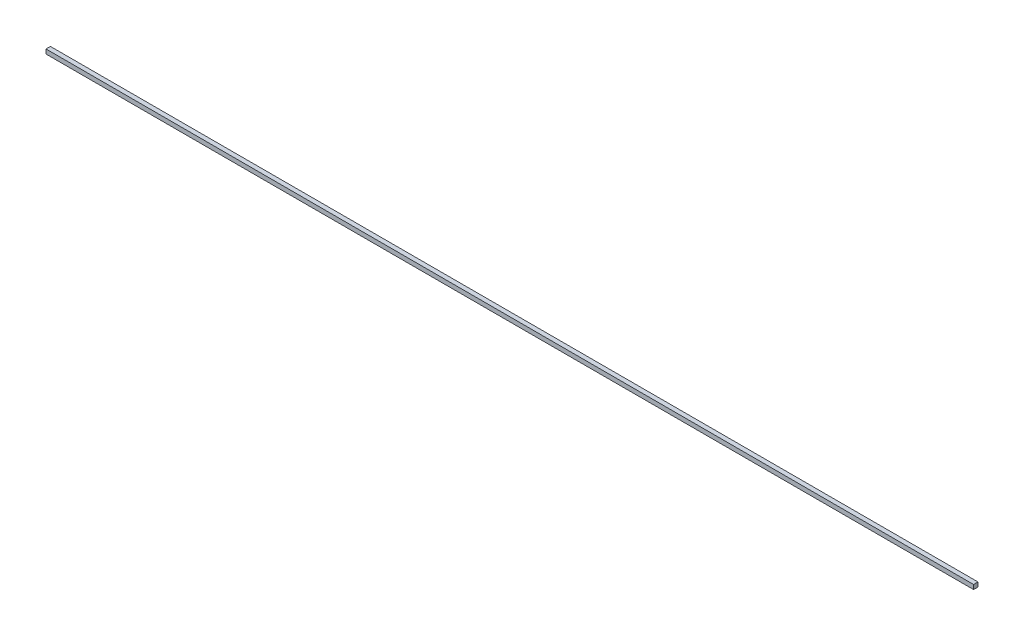
SolidWorks part; units mm, degrees
material "Nylon 6/10"
ref_plane "Front Plane" through (0, 0, 0) normal (0, 0, 1) x (1, 0, 0)
ref_plane "Top Plane" through (0, 0, 0) normal (0, 1, 0) x (1, 0, 0)
ref_plane "Right Plane" through (0, 0, 0) normal (1, 0, 0) x (0, 0, -1)
sketch "Sketch2" plane through (0, 0, 0) normal (0, 1, 0) x (1, 0, 0)
  line L5 (666.75, -3.175) -> (-666.75, -3.175)
  line L6 (666.75, -3.175) -> (666.75, 3.175)
  line L7 (666.75, 3.175) -> (-666.75, 3.175)
  line L8 (-666.75, -3.175) -> (-666.75, 3.175)
  line L9 (666.75, -3.175) -> (-666.75, 3.175) construction
  line L10 (666.75, 3.175) -> (-666.75, -3.175) construction
  point P0 (0, 0)
  dimension "D1" = 1333.5
  dimension "D2" = 6.35
extrude "Boss-Extrude2" add sketch "Sketch2" along normal blind 6.35
